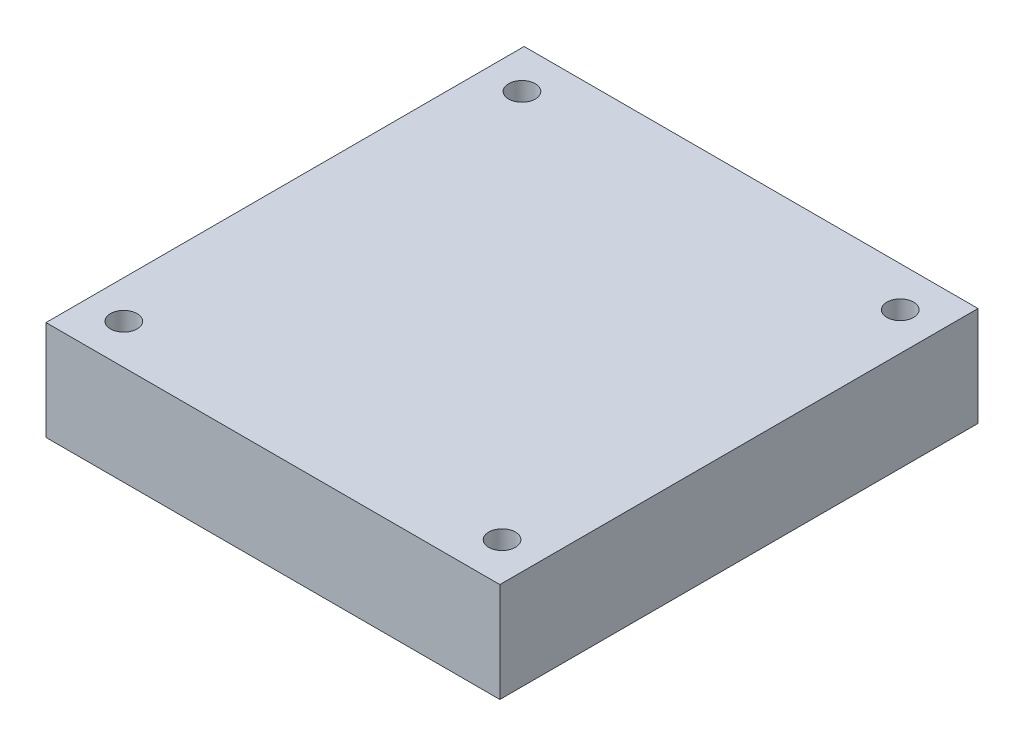
SolidWorks part; units mm, degrees
ref_plane "Front Plane" through (0, 0, 0) normal (0, 0, 1) x (1, 0, 0)
ref_plane "Top Plane" through (0, 0, 0) normal (0, 1, 0) x (1, 0, 0)
ref_plane "Right Plane" through (0, 0, 0) normal (1, 0, 0) x (0, 0, -1)
sketch "Sketch1" plane through (0, 0, 0) normal (0, 1, 0) x (1, 0, 0)
  line L1 (-28.95, 30.5) -> (28.95, 30.5)
  line L2 (-28.95, 30.5) -> (-28.95, -30.5)
  line L3 (-28.95, -30.5) -> (28.95, -30.5)
  line L4 (28.95, 30.5) -> (28.95, -30.5)
  dimension "D1" = 28.95
  dimension "D2" = 57.9
  dimension "D3" = 30.5
  dimension "D4" = 61
extrude "Extrude1" add sketch "Sketch1" along normal blind 12.7
sketch "Sketch10" plane through (0, 0, 0) normal (0, -1, 0) x (1, 0, 0)
  line L0 (-28.95, 30.5) -> (28.95, 30.5) construction
  line L1 (28.95, 30.5) -> (28.95, -30.5) construction
  line L2 (-28.95, 30.5) -> (28.95, 30.5) construction
  line L4 (-28.95, -30.5) -> (-28.95, 30.5) construction
  line L6 (28.95, -30.5) -> (-28.95, -30.5) construction
  line L7 (28.95, 30.5) -> (28.95, -30.5) construction
  circle A0 centre (24.13, 25.4) radius 1.7
  circle A1 centre (-24.13, 25.4) radius 1.7
  circle A2 centre (-24.13, -25.4) radius 1.7
  circle A3 centre (24.13, -25.4) radius 1.7
  dimension "D1" = 5.1
  dimension "D3" = 5.1
  dimension "D2" = 4.82
  dimension "D4" = 4.82
  dimension "D5" = 5.1
  dimension "D6" = 4.82
  dimension "D7" = 5.1
  dimension "D8" = 4.82
  dimension "D9" = 50.8
  dimension "D10" = 48.26
hole_wizard "M3 Clearance Hole1" positions "3DSketch2" profile "Sketch12" hole size "M3" standard "Ansi Metric"
sketch3d "3DSketch2"
  point P0 (24.13, 0, -25.4)
  point P3 (-24.13, 0, -25.4)
  point P6 (-24.13, 0, 25.4)
  point P9 (24.13, 0, 25.4)
sketch "Sketch12" plane through (24.13, 0, -25.4) normal (1, 0, 0) x (0, 0, -1)
  line L0 (0, 0) -> (0, 13.7215)
  line L1 (0, 13.7215) -> (1.7, 12.7)
  line L2 (1.7, 12.7) -> (1.7, 0)
  line L5 (1.7, 0) -> (0, 0)
  line L10 (0, 13.7215) -> (-1.7, 12.7) construction
  line L11 (0, -6.35) -> (0, 107.95) construction
  dimension "Hole Dia." = 3.4
  dimension "Hole Depth" = 12.7
  dimension "Drill Angle" = 118
